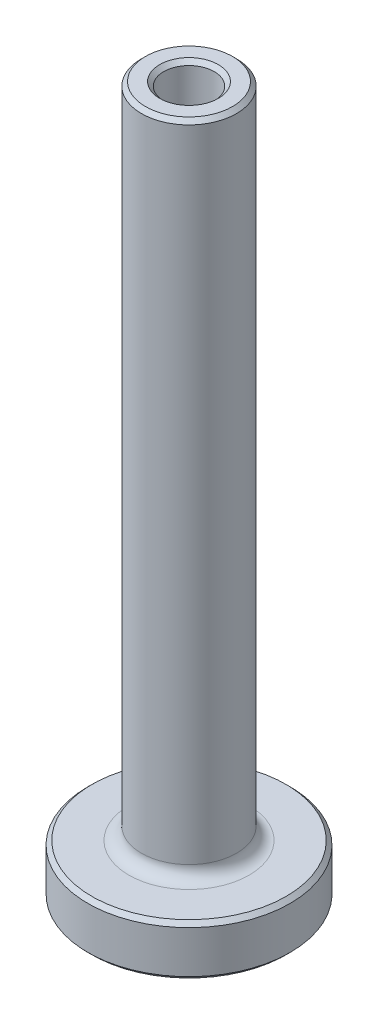
SolidWorks part; units mm, degrees
ref_plane "Front" through (0, 0, 0) normal (0, 0, 1) x (1, 0, 0)
ref_plane "Top" through (0, 0, 0) normal (0, 1, 0) x (1, 0, 0)
ref_plane "Right" through (0, 0, 0) normal (1, 0, 0) x (0, 0, -1)
sketch "Sketch1" plane through (0, 0, 0) normal (0, 0, 1) x (1, 0, 0)
  line L0 (0, 5.2992) -> (0, -5.2992) construction
  line L1 (2.286, 0) -> (2.286, 12.7)
  line L2 (2.286, 12.7) -> (1.5875, 12.7)
  line L3 (1.5875, 12.7) -> (1.5875, 44.45)
  line L4 (1.5875, 44.45) -> (2.9845, 44.45)
  line L5 (2.9845, 44.45) -> (2.9845, 3.175)
  line L6 (2.9845, 3.175) -> (6.35, 3.175)
  line L7 (6.35, 3.175) -> (6.35, 0)
  line L8 (6.35, 0) -> (2.286, 0)
  point P11 (2.4676, 0.7598)
  dimension "D1" = 12.7
  dimension "D2" = 3.175
  dimension "D3" = 4.572
  dimension "D4" = 5.969
  dimension "D5" = 3.175
  dimension "D6" = 41.275
  dimension "D7" = 31.75
revolve "Revolve1" add sketch "Sketch1" angle 360 about L0
fillet "Fillet1" radius 0.3969 1 edges at (-2.286, 12.7, 0)
fillet "Fillet2" radius 0.7937 1 edges at (-2.9845, 3.175, 0)
chamfer "Chamfer1" distance 0.254 angle 45 5 edges at (-2.286, 0, 0) (-6.35, 0, 0) (-2.9845, 44.45, 0) (-1.5875, 44.45, 0) (-6.35, 3.175, 0)
chamfer "Chamfer2" distance 0.127 angle 45 1 edges at (-1.5875, 12.7, 0)
